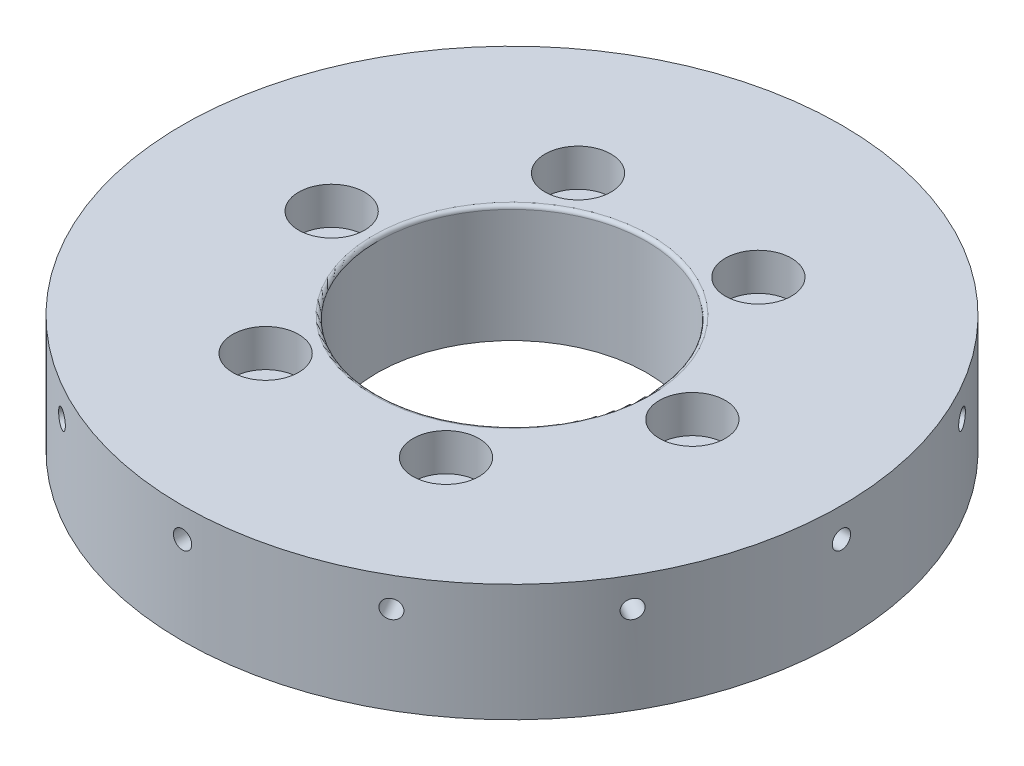
SolidWorks part; units mm, degrees
ref_plane "前视基准面" through (0, 0, 0) normal (0, 0, 1) x (1, 0, 0)
ref_plane "上视基准面" through (0, 0, 0) normal (0, 1, 0) x (1, 0, 0)
ref_plane "右视基准面" through (0, 0, 0) normal (1, 0, 0) x (0, 0, -1)
sketch "草图1" plane through (0, 0, 0) normal (0, 1, 0) x (1, 0, 0)
  circle A0 centre (0, 0) radius 44.95
  circle A1 centre (0, 0) radius 24.6 construction
  circle A2 centre (-24.6, 0) radius 2.1
  circle A3 centre (-12.3, 21.3042) radius 2.1
  circle A4 centre (12.3, 21.3042) radius 2.1
  circle A5 centre (24.6, 0) radius 2.1
  circle A6 centre (12.3, -21.3042) radius 2.1
  circle A7 centre (-12.3, -21.3042) radius 2.1
  circle A8 centre (0, 0) radius 18.4
  point P19 (0, 0)
  dimension "D1" = 6
  dimension "D2" = 89.9
extrude "凸台-拉伸1" add sketch "草图1" along normal blind 16
sketch "草图2" plane through (0, 0, 0) normal (0, -1, 0) x (1, 0, 0)
  circle A0 centre (0, 0) radius 24.6 construction
  circle A1 centre (-21.3042, -12.3) radius 4
  circle A2 centre (0, 24.6) radius 4
  circle A3 centre (21.3042, -12.3) radius 4
  point P17 (0, 0)
  dimension "D1" = 3
extrude "切除-拉伸1" cut sketch "草图2" against normal blind 3
sketch "草图4" plane through (0, 16, 0) normal (0, 1, 0) x (1, 0, 0)
  circle A0 centre (-24.6, 0) radius 4.5
  circle A1 centre (0, 0) radius 24.6 construction
  circle A2 centre (-12.3, 21.3042) radius 4.5
  circle A3 centre (12.3, 21.3042) radius 4.5
  circle A4 centre (24.6, 0) radius 4.5
  circle A5 centre (12.3, -21.3042) radius 4.5
  circle A6 centre (-12.3, -21.3042) radius 4.5
  point P16 (0, 0)
  dimension "D1" = 6
extrude "切除-拉伸2" cut sketch "草图4" against normal blind 5.1
ref_plane "基准面1" through (45, 0, 0) normal (1, 0, 0) x (0, 0, -1)
sketch "草图5" plane through (45, 0, 0) normal (1, 0, 0) x (0, 0, -1)
  circle A0 centre (0, 12) radius 1.25
extrude "切除-拉伸3" cut sketch "草图5" against normal blind 10
pattern_circular "阵列(圆周)1" count 12 every 30 about axis through (0, 0, 0) along (0, 1, 0) of "切除-拉伸3"
fillet "圆角1" radius 0.5 1 edges at (0, 16, 18.4)
